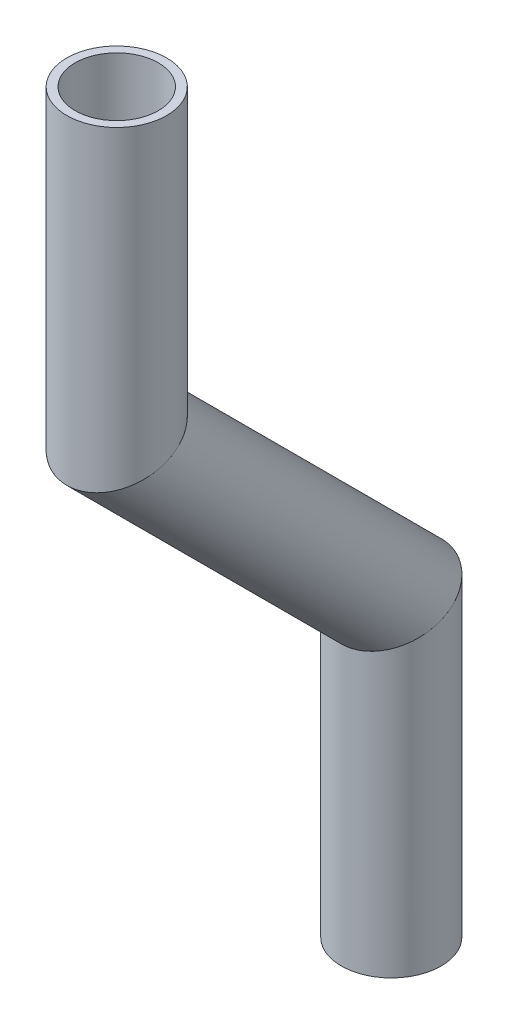
SolidWorks part; units mm, degrees
ref_plane "Front Plane" through (0, 0, 0) normal (0, 0, 1) x (1, 0, 0)
ref_plane "Top Plane" through (0, 0, 0) normal (0, 1, 0) x (1, 0, 0)
ref_plane "Right Plane" through (0, 0, 0) normal (1, 0, 0) x (0, 0, -1)
sketch "Sketch1" plane through (0, 0, 0) normal (1, 0, 0) x (0, 0, -1)
  line L0 (-362.7653, -435.3411) -> (-362.7653, -473.4411)
  line L1 (-362.7653, -473.4411) -> (-327.8546, -508.3518)
  line L2 (-327.8546, -508.3518) -> (-327.8546, -546.4518)
  line L3 (-362.7653, -473.4411) -> (-362.7653, -499.5396) construction
  dimension "D1" = 45
  dimension "D2" = 38.1
  dimension "D3" = 38.1
other "Pipe 0.5 SCH 40(1)"
ref_plane "Plane1" through (0, -435.3411, 362.7653) normal (0, -1, 0) x (0, 0, -1)
sketch "Sketch11" plane through (0, -435.3411, 362.7653) normal (0, -1, 0) x (0, 0, -1)
  circle A0 centre (0, 0) radius 5.2832
  circle A1 centre (0, 0) radius 6.35
  point P5 (0, 0)
  dimension "In_dia" = 10.5664
  dimension "Out_dia" = 12.7
